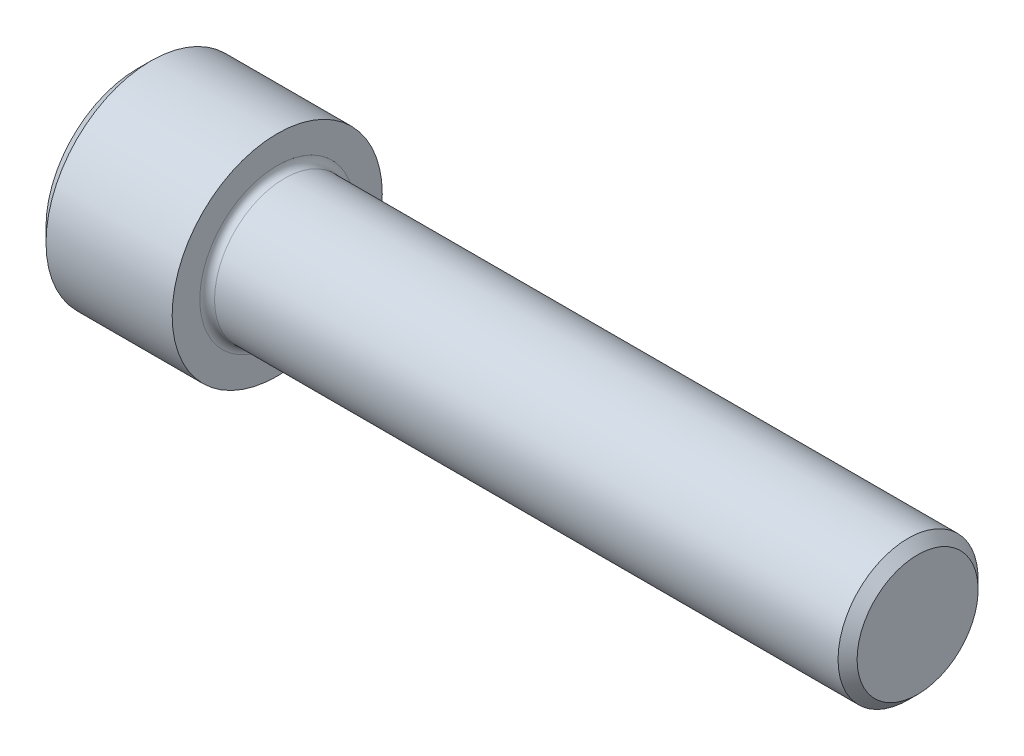
SolidWorks part; units mm, degrees
revolve "Base-Revolve" add sketch "BodySke"
sketch "BodySke" plane through (0, 0, 0) normal (0, 0, 1) x (1, 0, 0)
  line L0 (0, 0) -> (0, 7.2301)
  line L1 (1.1049, 8.335) -> (11.1125, 8.335)
  line L2 (11.1125, 8.335) -> (11.1125, 5.5563)
  line L3 (11.1125, 5.5563) -> (61.1569, 5.5563)
  line L4 (61.9125, 4.8006) -> (61.9125, 0)
  line L5 (61.9125, 0) -> (0, 0)
  line L6 (-31.75, 0) -> (127, 0) construction
  line L7 (0, 7.2301) -> (1.1049, 8.335)
  line L8 (61.9125, 4.8006) -> (61.1569, 5.5563)
  line L9 (0, -7.2301) -> (1.1049, -8.335) construction
  line L10 (61.9125, -4.8006) -> (61.1569, -5.5562) construction
  line L11 (12.3825, 9.525) -> (12.3825, 3.175) construction
  line L12 (26.9875, 9.525) -> (26.9875, 3.175) construction
  line L13 (23.8125, 9.525) -> (23.8125, 3.175) construction
  dimension "Diameter" = 11.1125
  dimension "Head_ht" = 11.1125
  dimension "Length" = 50.8
  dimension "Body_ch_ang" = 45
  dimension "Head_dia" = 16.67
  dimension "Head_ch_ang" = 45
  dimension "Head_side_ht" = 10.0076
  dimension "Minor_dia" = 9.6012
  dimension "Advance" = 1.27
  dimension "Thread_nom" = 34.925
  dimension "Thread_length" = 38.1
cosmetic thread "ThreadCosmetic" [suppressed]
fillet "Fillet1" radius 0.5842 1 edges at (11.1125, 0, 5.5563)
ref_plane "Plane1" through (0, 0, 0) normal (0, 0, 1) x (1, 0, 0)
ref_plane "Plane2" through (0, 0, 0) normal (0, 1, 0) x (1, 0, 0)
ref_plane "Plane3" through (0, 0, 0) normal (1, 0, 0) x (0, 0, -1)
other "Configuration Table"
sketch "Sketch2" plane through (0, 0, 0) normal (0, 0, 1) x (1, 0, 0)
  line L0 (0, 4.7625) -> (5.4102, 4.7625)
  line L1 (5.4102, 4.7625) -> (8.1598, 0)
  line L2 (-31.75, 0) -> (127, 0) construction
  line L3 (8.1598, 0) -> (0, 0)
  line L4 (0, 0) -> (0, 4.7625)
  line L5 (0, 7.2301) -> (0, -7.2301) construction
  line L6 (0, 0) -> (47.625, 0) construction
  line L7 (11.1125, -8.335) -> (11.1125, 8.335) construction
  dimension "D2" = 60
revolve "Hex-PreBroach" cut sketch "Sketch2" angle 360 about L6
sketch "Sketch3" plane through (0, 0, 0) normal (-1, 0, 0) x (0, 0.5, 0.866)
  line L0 (2.7496, 4.7625) -> (-2.7496, 4.7625)
  line L1 (-2.7496, 4.7625) -> (-5.4993, 0)
  line L2 (2.7496, 4.7625) -> (5.4993, 0)
  line L3 (2.7496, -4.7625) -> (5.4993, 0)
  line L4 (2.7496, -4.7625) -> (-2.7496, -4.7625)
  line L5 (-2.7496, -4.7625) -> (-5.4993, 0)
extrude "Hex" cut sketch "Sketch3" against normal blind 5.4102
sketch "Sketch4" plane through (0, 0, 0) normal (-1, 0, 0) x (0, 0, 1)
  line L0 (0, 0) -> (5.8801, 0)
  line L1 (0, 0) -> (6.1484, 3.5498) construction
  line L2 (0, 0) -> (2.94, 5.0923)
  line L3 (4.774, 1.1138) -> (5.6523, 1.6209)
  line L4 (3.3516, 3.5775) -> (4.2299, 4.0846)
  arc A0 (4.774, 1.1138) -> (3.3516, 3.5775) centre (0, 0) ccw
  arc A1 (5.8801, 0) -> (5.6523, 1.6209) centre (0, 0) ccw
  arc A2 (2.94, 5.0923) -> (4.2299, 4.0846) centre (0, 0) cw
  dimension "D1" = 30
  dimension "D2" = 60
extrude "Spline" [suppressed] cut sketch "Sketch4" against normal blind 5.4102
pattern_circular "CirPattern1" [suppressed] count 6 every 60
sketch "Sketch5" plane through (0, 0, 0) normal (0, 0, 1) x (1, 0, 0)
  line L0 (-31.75, 0) -> (127, 0) construction
  line L2 (0, 7.2301) -> (0, -7.2301) construction
  circle A0 centre (3.5814, 0) radius 0.8065
  dimension "Drilled_hole_dia" = 1.6129
  dimension "Drilled_hole_loc" = 3.5814
extrude "Hole" [suppressed] cut sketch "Sketch5" against normal through all and the other way through all
pattern_circular "Drilled-4" [suppressed] count 2 every 60
pattern_circular "Drilled-6" [suppressed] count 3 every 60
sketch "ThdSchSke" plane through (0, 0, 0) normal (0, 0, 1) x (1, 0, 0)
  line L0 (26.9875, -4.8006) -> (26.4584, -5.5562)
  line L1 (26.9875, -4.8006) -> (27.5166, -5.5562)
  line L2 (27.5166, -5.5562) -> (27.5166, -6.9453)
  line L3 (-3.175, 0) -> (5.1513, 0) construction
  line L5 (27.5166, -6.9453) -> (26.4584, -6.9453)
  line L6 (26.4584, -6.9453) -> (26.4584, -5.5562)
  line L7 (0, 7.2301) -> (0, -7.2301) construction
revolve "ThreadSchematic" [suppressed] cut sketch "ThdSchSke" angle 360 about L3
pattern_linear "ThdSchPat" [suppressed]
equation "\"D2@Sketch3\" = \"Hex_size@Sketch3\" / 2"
equation "\"D1@Sketch3\" = \"Hex_size@Sketch3\" / 2"
equation "\"D1@Sketch2\" = \"Hex_size@Sketch3\" / 2"
equation "\"D3@Sketch4\" = \"Spline_p_dim@Sketch4\" / 2"
equation "\"Thread_minor@ThreadCosmetic\"  =  \"Minor_dia@BodySke\""
equation "\"D2@CirPattern1\" = 360 / \"Num_teeth@CirPattern1\""
equation "\"Wall_thickness@Sketch2\" = \"Head_ht@BodySke\" - \"Key_eng@Hex\""
equation "\"Thread_length@ThreadCosmetic\" = ((sgn( (\"Length@BodySke\" - \"Advance@BodySke\" ) - \"Thread_nom@BodySke\" )-1)*( (\"Length@BodySke\" - \"Advance@BodySke\" ) - \"Thread_nom@BodySke\" ))/-2+ \"Thread_nom@BodySke\""
equation "\"Thread_minor@ThdSchSke\" = \"Minor_dia@BodySke\""
equation "\"Diameter@ThdSchSke\" = \"Diameter@BodySke\""
equation "\"Overcut@ThdSchSke\" = \"Diameter@BodySke\" * 1.25"
equation "\"Start@ThdSchSke\" = \"Head_ht@BodySke\" + \"Length@BodySke\" - \"Thread_length@ThreadCosmetic\"  '---Non-countersunk---"
equation "\"Num_threads@ThdSchPat\" = int( \"Thread_length@ThreadCosmetic\" / \"Advance@BodySke\" + 0.999 )  + 1"
equation "\"Advance@ThdSchPat\" = \"Thread_length@ThreadCosmetic\" /  (\"Num_threads@ThdSchPat\" - 1) 'relax it"
equation "\"Num_threads@ThdSchPat\" = \"Num_threads@ThdSchPat\" - sgn( \"Num_threads@ThdSchPat\" - 1) '---chamfered tips only---"
